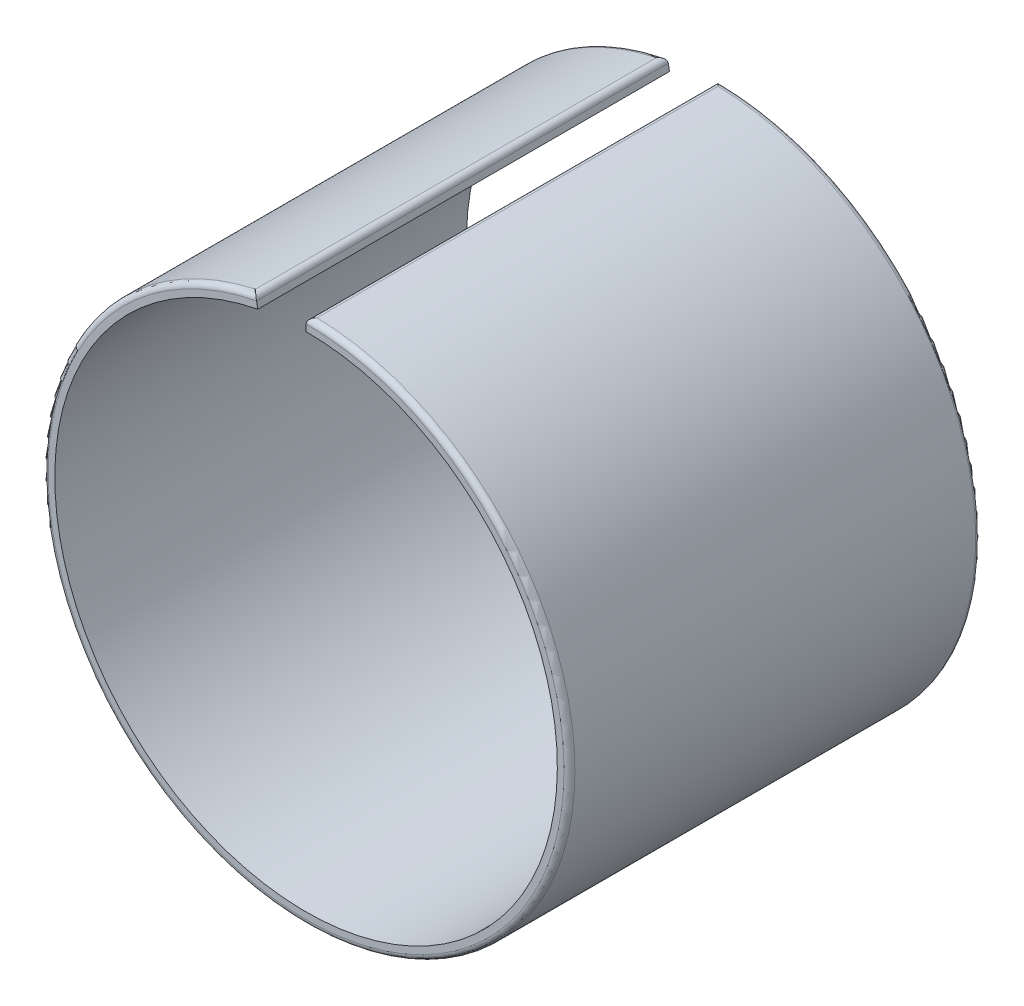
SolidWorks part; units mm, degrees
ref_plane "Front Plane" through (0, 0, 0) normal (0, 0, 1) x (1, 0, 0)
ref_plane "Top Plane" through (0, 0, 0) normal (0, 1, 0) x (1, 0, 0)
ref_plane "Right Plane" through (0, 0, 0) normal (1, 0, 0) x (0, 0, -1)
sketch "Sketch4" plane through (0, 0, 0) normal (0, 0, 1) x (1, 0, 0)
  line L0 (0, 20.75) -> (0, 21.75)
  line L1 (-3.9814, 20.3645) -> (-4.1732, 21.3459)
  arc A0 (-3.9814, 20.3645) -> (0, 20.75) centre (0, 0) ccw
  arc A1 (-4.1732, 21.3459) -> (0, 21.75) centre (0, 0) ccw
  circle A2 centre (0, 0) radius 20.75 construction
  circle A3 centre (0, 0) radius 21.75 construction
  point P7 (-3.9814, 20.3645)
  dimension "D1" = 41.5
  dimension "D3" = 4
  dimension "D2" = 1
extrude "Boss-Extrude3" add sketch "Sketch4" along normal blind 34
fillet "Fillet2" radius 0.45 4 edges at (-4.1732, 21.3459, 17) (2.0964, -21.6487, 34) (0, 21.75, 17) (2.0964, -21.6487, 0)
